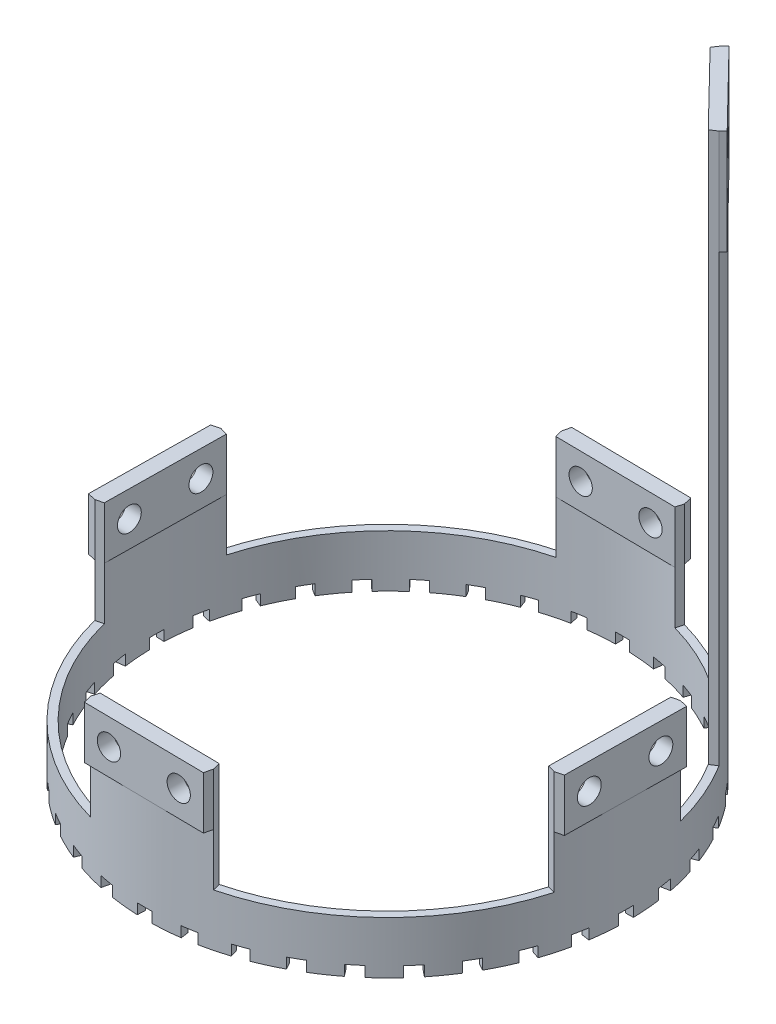
SolidWorks part; units mm, degrees
ref_plane "前视基准面" through (0, 0, 0) normal (0, 0, 1) x (1, 0, 0)
ref_plane "上视基准面" through (0, 0, 0) normal (0, 1, 0) x (1, 0, 0)
ref_plane "右视基准面" through (0, 0, 0) normal (1, 0, 0) x (0, 0, -1)
sketch "草图1" plane through (0, 0, 0) normal (0, 1, 0) x (1, 0, 0)
  circle A0 centre (0, 0) radius 46
  circle A1 centre (0, 0) radius 44.5
  dimension "D1" = 92
  dimension "D2" = 89
extrude "凸台-拉伸1" add sketch "草图1" along normal blind 10
sketch "草图2" plane through (0, 10, 0) normal (0, 1, 0) x (1, 0, 0)
  line L0 (-10.9731, 43.1259) -> (-11.343, 44.5796)
  line L1 (12.06, 42.8347) -> (12.4665, 44.2785)
  line L2 (43.1259, 10.9731) -> (44.5796, 11.343)
  line L3 (42.8347, -12.06) -> (44.2785, -12.4665)
  line L4 (10.9731, -43.1259) -> (11.343, -44.5796)
  line L5 (-12.06, -42.8347) -> (-12.4665, -44.2785)
  line L6 (-43.1259, -10.9731) -> (-44.5796, -11.343)
  line L7 (-42.8347, 12.06) -> (-44.2785, 12.4665)
  arc A0 (12.06, 42.8347) -> (-10.9731, 43.1259) centre (0, 0) ccw
  arc A1 (12.4665, 44.2785) -> (-11.343, 44.5796) centre (0, 0) ccw
  arc A2 (42.8347, -12.06) -> (43.1259, 10.9731) centre (0, 0) ccw
  arc A3 (44.2785, -12.4665) -> (44.5796, 11.343) centre (0, 0) ccw
  arc A4 (-12.06, -42.8347) -> (10.9731, -43.1259) centre (0, 0) ccw
  arc A5 (-12.4665, -44.2785) -> (11.343, -44.5796) centre (0, 0) ccw
  arc A6 (-42.8347, 12.06) -> (-43.1259, -10.9731) centre (0, 0) ccw
  arc A7 (-44.2785, 12.4665) -> (-44.5796, -11.343) centre (0, 0) ccw
  point P21 (0, 0)
  dimension "D1" = 30
  dimension "D2" = 4
extrude "凸台-拉伸2" add sketch "草图2" along normal blind 20
sketch "草图3" plane through (0, 30, 0) normal (0, 1, 0) x (1, 0, 0)
  line L16 (-10.9731, 46.1424) -> (-11.343, 44.5796)
  line L17 (-11.343, 44.5796) -> (-10.9731, 43.1259)
  line L18 (12.06, 45.8512) -> (12.4665, 44.2785)
  line L19 (12.06, 42.8347) -> (12.4665, 44.2785) construction
  line L20 (12.4665, 44.2785) -> (12.06, 42.8347)
  line L22 (44.2785, -12.4665) -> (42.8347, -12.06)
  line L23 (45.8512, -12.06) -> (44.2785, -12.4665)
  line L25 (46.1424, 10.9731) -> (44.5796, 11.343)
  line L26 (44.5796, 11.343) -> (43.1259, 10.9731)
  line L28 (-12.4665, -44.2785) -> (-12.06, -42.8347)
  line L29 (-12.06, -45.8512) -> (-12.4665, -44.2785)
  line L31 (10.9731, -46.1424) -> (11.343, -44.5796)
  line L32 (11.343, -44.5796) -> (10.9731, -43.1259)
  line L34 (-44.2785, 12.4665) -> (-42.8347, 12.06)
  line L35 (-45.8512, 12.06) -> (-44.2785, 12.4665)
  line L37 (-46.1424, -10.9731) -> (-44.5796, -11.343)
  line L38 (-44.5796, -11.343) -> (-43.1259, -10.9731)
  line L39 (-10.9731, 46.1424) -> (12.06, 45.8512)
  line L40 (12.06, 42.8347) -> (-10.9731, 43.1259)
  line L41 (-42.8347, 12.06) -> (-43.1259, -10.9731)
  line L42 (-46.1424, -10.9731) -> (-45.8512, 12.06)
  line L43 (10.9731, -43.1259) -> (-12.06, -42.8347)
  line L44 (-12.06, -45.8512) -> (10.9731, -46.1424)
  line L45 (43.1259, 10.9731) -> (42.8347, -12.06)
  line L46 (45.8512, -12.06) -> (46.1424, 10.9731)
  arc A0 (44.5796, 11.343) -> (12.4665, 44.2785) centre (0, 0) ccw construction
  point P24 (0, 0)
  point P51 (0, 0)
  dimension "D2" = 4
extrude "凸台-拉伸4" add sketch "草图3" against normal blind 10
sketch "草图5" plane through (-45.9963, 0, -0.5816) normal (-0.9999, 0, -0.0126) x (-0.0126, 0, 0.9999)
  line L0 (0.0381, 30) -> (0.0381, 5.2053) construction
  line L1 (-11.4793, 30) -> (11.5556, 30) construction
  line L2 (-46, 0) -> (46, 0) construction
  circle A0 centre (-6.7119, 25) radius 2.25
  circle A1 centre (6.7881, 25) radius 2.25
  dimension "D1" = 4.5
  dimension "D2" = 6.75
  dimension "D3" = 25
extrude "切除-拉伸1" cut sketch "草图5" against normal through all
sketch "草图6" plane through (-0.5816, 0, 45.9963) normal (-0.0126, 0, 0.9999) x (0.9999, 0, 0.0126)
  line L0 (0.0381, 30) -> (0, 0) construction
  line L1 (-11.4793, 30) -> (11.5556, 30) construction
  line L2 (-46, 0) -> (46, 0) construction
  circle A0 centre (-6.7182, 25) radius 2.25
  circle A1 centre (6.7818, 24.9828) radius 2.25
  dimension "D1" = 6.75
  dimension "D2" = 25
extrude "切除-拉伸2" cut sketch "草图6" against normal through all
sketch "草图7" plane through (0, 0, 0) normal (0, -1, 0) x (1, 0, 0)
  line L0 (-1.7737, 44.4646) -> (-1.8335, 45.9634)
  line L1 (0.9441, 44.49) -> (0.9759, 45.9896)
  line L2 (5.9744, 44.0971) -> (6.1758, 45.5835)
  line L3 (8.6553, 43.6501) -> (8.9471, 45.1215)
  line L4 (13.541, 42.3897) -> (13.9975, 43.8186)
  line L5 (16.1036, 41.484) -> (16.6464, 42.8824)
  line L6 (20.6962, 39.3944) -> (21.3938, 40.7223)
  line L7 (23.0626, 38.0574) -> (23.84, 39.3403)
  line L8 (27.2225, 35.202) -> (28.1402, 36.3886)
  line L9 (29.3208, 33.4745) -> (30.3091, 34.6028)
  line L10 (32.9217, 29.9401) -> (34.0315, 30.9493)
  line L11 (34.6881, 27.8744) -> (35.8574, 28.814)
  line L12 (37.6206, 23.7684) -> (38.8887, 24.5696)
  line L13 (39.0015, 21.4274) -> (40.3161, 22.1497)
  line L14 (41.1764, 16.8746) -> (42.5644, 17.4434)
  line L15 (42.1298, 14.3293) -> (43.5499, 14.8124)
  line L16 (43.4811, 9.468) -> (44.9468, 9.7871)
  line L17 (43.978, 6.7959) -> (45.4604, 7.025)
  line L18 (44.4646, 1.7737) -> (45.9634, 1.8335)
  line L19 (44.49, -0.9441) -> (45.9896, -0.9759)
  line L20 (44.0971, -5.9744) -> (45.5835, -6.1758)
  line L21 (43.6501, -8.6553) -> (45.1215, -8.9471)
  line L22 (42.3897, -13.541) -> (43.8186, -13.9975)
  line L23 (41.484, -16.1036) -> (42.8824, -16.6464)
  line L24 (39.3944, -20.6962) -> (40.7223, -21.3938)
  line L25 (38.0574, -23.0626) -> (39.3403, -23.84)
  line L26 (35.202, -27.2225) -> (36.3886, -28.1402)
  line L27 (33.4745, -29.3208) -> (34.6028, -30.3091)
  line L28 (29.9401, -32.9217) -> (30.9493, -34.0315)
  line L29 (27.8744, -34.6881) -> (28.814, -35.8574)
  line L30 (23.7684, -37.6206) -> (24.5696, -38.8887)
  line L31 (21.4274, -39.0015) -> (22.1497, -40.3161)
  line L32 (16.8746, -41.1764) -> (17.4434, -42.5644)
  line L33 (14.3293, -42.1298) -> (14.8124, -43.5499)
  line L34 (9.468, -43.4811) -> (9.7871, -44.9468)
  line L35 (6.7959, -43.978) -> (7.025, -45.4604)
  line L36 (1.7737, -44.4646) -> (1.8335, -45.9634)
  line L37 (-0.9441, -44.49) -> (-0.9759, -45.9896)
  line L38 (-5.9744, -44.0971) -> (-6.1758, -45.5835)
  line L39 (-8.6553, -43.6501) -> (-8.9471, -45.1215)
  line L40 (-13.541, -42.3897) -> (-13.9975, -43.8186)
  line L41 (-16.1036, -41.484) -> (-16.6464, -42.8824)
  line L42 (-20.6962, -39.3944) -> (-21.3938, -40.7223)
  line L43 (-23.0626, -38.0574) -> (-23.84, -39.3403)
  line L44 (-27.2225, -35.202) -> (-28.1402, -36.3886)
  line L45 (-29.3208, -33.4745) -> (-30.3091, -34.6028)
  line L46 (-32.9217, -29.9401) -> (-34.0315, -30.9493)
  line L47 (-34.6881, -27.8744) -> (-35.8574, -28.814)
  line L48 (-37.6206, -23.7684) -> (-38.8887, -24.5696)
  line L49 (-39.0015, -21.4274) -> (-40.3161, -22.1497)
  line L50 (-41.1764, -16.8746) -> (-42.5644, -17.4434)
  line L51 (-42.1298, -14.3293) -> (-43.5499, -14.8124)
  line L52 (-43.4811, -9.468) -> (-44.9468, -9.7871)
  line L53 (-43.978, -6.7959) -> (-45.4604, -7.025)
  line L54 (-44.4646, -1.7737) -> (-45.9634, -1.8335)
  line L55 (-44.49, 0.9441) -> (-45.9896, 0.9759)
  line L56 (-44.0971, 5.9744) -> (-45.5835, 6.1758)
  line L57 (-43.6501, 8.6553) -> (-45.1215, 8.9471)
  line L58 (-42.3897, 13.541) -> (-43.8186, 13.9975)
  line L59 (-41.484, 16.1036) -> (-42.8824, 16.6464)
  line L60 (-39.3944, 20.6962) -> (-40.7223, 21.3938)
  line L61 (-38.0574, 23.0626) -> (-39.3403, 23.84)
  line L62 (-35.202, 27.2225) -> (-36.3886, 28.1402)
  line L63 (-33.4745, 29.3208) -> (-34.6028, 30.3091)
  line L64 (-29.9401, 32.9217) -> (-30.9493, 34.0315)
  line L65 (-27.8744, 34.6881) -> (-28.814, 35.8574)
  line L66 (-23.7684, 37.6206) -> (-24.5696, 38.8887)
  line L67 (-21.4274, 39.0015) -> (-22.1497, 40.3161)
  line L68 (-16.8746, 41.1764) -> (-17.4434, 42.5644)
  line L69 (-14.3293, 42.1298) -> (-14.8124, 43.5499)
  line L70 (-9.468, 43.4811) -> (-9.7871, 44.9468)
  line L71 (-6.7959, 43.978) -> (-7.025, 45.4604)
  circle A0 centre (0, 0) radius 46 construction
  arc A1 (0.9441, 44.49) -> (-1.7737, 44.4646) centre (0, 0) ccw
  arc A2 (0.9759, 45.9896) -> (-1.8335, 45.9634) centre (0, 0) ccw
  arc A3 (8.9471, 45.1215) -> (6.1758, 45.5835) centre (0, 0) ccw
  arc A4 (8.6553, 43.6501) -> (5.9744, 44.0971) centre (0, 0) ccw
  arc A5 (16.6464, 42.8824) -> (13.9975, 43.8186) centre (0, 0) ccw
  arc A6 (16.1036, 41.484) -> (13.541, 42.3897) centre (0, 0) ccw
  arc A7 (23.84, 39.3403) -> (21.3938, 40.7223) centre (0, 0) ccw
  arc A8 (23.0626, 38.0574) -> (20.6962, 39.3944) centre (0, 0) ccw
  arc A9 (30.3091, 34.6028) -> (28.1402, 36.3886) centre (0, 0) ccw
  arc A10 (29.3208, 33.4745) -> (27.2225, 35.202) centre (0, 0) ccw
  arc A11 (35.8574, 28.814) -> (34.0315, 30.9493) centre (0, 0) ccw
  arc A12 (34.6881, 27.8744) -> (32.9217, 29.9401) centre (0, 0) ccw
  arc A13 (40.3161, 22.1497) -> (38.8887, 24.5696) centre (0, 0) ccw
  arc A14 (39.0015, 21.4274) -> (37.6206, 23.7684) centre (0, 0) ccw
  arc A15 (43.5499, 14.8124) -> (42.5644, 17.4434) centre (0, 0) ccw
  arc A16 (42.1298, 14.3293) -> (41.1764, 16.8746) centre (0, 0) ccw
  arc A17 (45.4604, 7.025) -> (44.9468, 9.7871) centre (0, 0) ccw
  arc A18 (43.978, 6.7959) -> (43.4811, 9.468) centre (0, 0) ccw
  arc A19 (45.9896, -0.9759) -> (45.9634, 1.8335) centre (0, 0) ccw
  arc A20 (44.49, -0.9441) -> (44.4646, 1.7737) centre (0, 0) ccw
  arc A21 (45.1215, -8.9471) -> (45.5835, -6.1758) centre (0, 0) ccw
  arc A22 (43.6501, -8.6553) -> (44.0971, -5.9744) centre (0, 0) ccw
  arc A23 (42.8824, -16.6464) -> (43.8186, -13.9975) centre (0, 0) ccw
  arc A24 (41.484, -16.1036) -> (42.3897, -13.541) centre (0, 0) ccw
  arc A25 (39.3403, -23.84) -> (40.7223, -21.3938) centre (0, 0) ccw
  arc A26 (38.0574, -23.0626) -> (39.3944, -20.6962) centre (0, 0) ccw
  arc A27 (34.6028, -30.3091) -> (36.3886, -28.1402) centre (0, 0) ccw
  arc A28 (33.4745, -29.3208) -> (35.202, -27.2225) centre (0, 0) ccw
  arc A29 (28.814, -35.8574) -> (30.9493, -34.0315) centre (0, 0) ccw
  arc A30 (27.8744, -34.6881) -> (29.9401, -32.9217) centre (0, 0) ccw
  arc A31 (22.1497, -40.3161) -> (24.5696, -38.8887) centre (0, 0) ccw
  arc A32 (21.4274, -39.0015) -> (23.7684, -37.6206) centre (0, 0) ccw
  arc A33 (14.8124, -43.5499) -> (17.4434, -42.5644) centre (0, 0) ccw
  arc A34 (14.3293, -42.1298) -> (16.8746, -41.1764) centre (0, 0) ccw
  arc A35 (7.025, -45.4604) -> (9.7871, -44.9468) centre (0, 0) ccw
  arc A36 (6.7959, -43.978) -> (9.468, -43.4811) centre (0, 0) ccw
  arc A37 (-0.9759, -45.9896) -> (1.8335, -45.9634) centre (0, 0) ccw
  arc A38 (-0.9441, -44.49) -> (1.7737, -44.4646) centre (0, 0) ccw
  arc A39 (-8.9471, -45.1215) -> (-6.1758, -45.5835) centre (0, 0) ccw
  arc A40 (-8.6553, -43.6501) -> (-5.9744, -44.0971) centre (0, 0) ccw
  arc A41 (-16.6464, -42.8824) -> (-13.9975, -43.8186) centre (0, 0) ccw
  arc A42 (-16.1036, -41.484) -> (-13.541, -42.3897) centre (0, 0) ccw
  arc A43 (-23.84, -39.3403) -> (-21.3938, -40.7223) centre (0, 0) ccw
  arc A44 (-23.0626, -38.0574) -> (-20.6962, -39.3944) centre (0, 0) ccw
  arc A45 (-30.3091, -34.6028) -> (-28.1402, -36.3886) centre (0, 0) ccw
  arc A46 (-29.3208, -33.4745) -> (-27.2225, -35.202) centre (0, 0) ccw
  arc A47 (-35.8574, -28.814) -> (-34.0315, -30.9493) centre (0, 0) ccw
  arc A48 (-34.6881, -27.8744) -> (-32.9217, -29.9401) centre (0, 0) ccw
  arc A49 (-40.3161, -22.1497) -> (-38.8887, -24.5696) centre (0, 0) ccw
  arc A50 (-39.0015, -21.4274) -> (-37.6206, -23.7684) centre (0, 0) ccw
  arc A51 (-43.5499, -14.8124) -> (-42.5644, -17.4434) centre (0, 0) ccw
  arc A52 (-42.1298, -14.3293) -> (-41.1764, -16.8746) centre (0, 0) ccw
  arc A53 (-45.4604, -7.025) -> (-44.9468, -9.7871) centre (0, 0) ccw
  arc A54 (-43.978, -6.7959) -> (-43.4811, -9.468) centre (0, 0) ccw
  arc A55 (-45.9896, 0.9759) -> (-45.9634, -1.8335) centre (0, 0) ccw
  arc A56 (-44.49, 0.9441) -> (-44.4646, -1.7737) centre (0, 0) ccw
  arc A57 (-45.1215, 8.9471) -> (-45.5835, 6.1758) centre (0, 0) ccw
  arc A58 (-43.6501, 8.6553) -> (-44.0971, 5.9744) centre (0, 0) ccw
  arc A59 (-42.8824, 16.6464) -> (-43.8186, 13.9975) centre (0, 0) ccw
  arc A60 (-41.484, 16.1036) -> (-42.3897, 13.541) centre (0, 0) ccw
  arc A61 (-39.3403, 23.84) -> (-40.7223, 21.3938) centre (0, 0) ccw
  arc A62 (-38.0574, 23.0626) -> (-39.3944, 20.6962) centre (0, 0) ccw
  arc A63 (-34.6028, 30.3091) -> (-36.3886, 28.1402) centre (0, 0) ccw
  arc A64 (-33.4745, 29.3208) -> (-35.202, 27.2225) centre (0, 0) ccw
  arc A65 (-28.814, 35.8574) -> (-30.9493, 34.0315) centre (0, 0) ccw
  arc A66 (-27.8744, 34.6881) -> (-29.9401, 32.9217) centre (0, 0) ccw
  arc A67 (-22.1497, 40.3161) -> (-24.5696, 38.8887) centre (0, 0) ccw
  arc A68 (-21.4274, 39.0015) -> (-23.7684, 37.6206) centre (0, 0) ccw
  arc A69 (-14.8124, 43.5499) -> (-17.4434, 42.5644) centre (0, 0) ccw
  arc A70 (-14.3293, 42.1298) -> (-16.8746, 41.1764) centre (0, 0) ccw
  arc A71 (-7.025, 45.4604) -> (-9.7871, 44.9468) centre (0, 0) ccw
  arc A72 (-6.7959, 43.978) -> (-9.468, 43.4811) centre (0, 0) ccw
  point P151 (0, 0)
  dimension "D1" = 3.5
  dimension "D2" = 36
extrude "切除-拉伸3" cut sketch "草图7" against normal blind 2
sketch "草图8" plane through (0, 10, 0) normal (0, 1, 0) x (1, 0, 0)
  line L0 (0, 0) -> (32.9355, 32.1131) construction
  line L1 (0, 0) -> (25.2043, 38.4804) construction
  line L2 (0, 0) -> (39.1054, 24.2233) construction
  line L3 (25.2043, 38.4804) -> (39.1054, 24.2233) construction
  line L4 (25.2043, 38.4804) -> (24.3824, 37.2256)
  line L5 (39.1054, 24.2233) -> (37.8302, 23.4334)
  arc A0 (44.5796, 11.343) -> (12.4665, 44.2785) centre (0, 0) ccw construction
  arc A1 (43.1259, 10.9731) -> (12.06, 42.8347) centre (0, 0) ccw construction
  arc A2 (37.8302, 23.4334) -> (24.3824, 37.2256) centre (0, 0) ccw
  arc A3 (39.1054, 24.2233) -> (25.2043, 38.4804) centre (0, 0) ccw
  dimension "D1" = 25
extrude "凸台-拉伸6" add sketch "草图8" along normal blind 105
sketch "草图9" plane through (0, 115, 0) normal (0, 1, 0) x (1, 0, 0)
  line L0 (24.3824, 37.2256) -> (37.8302, 23.4334)
  line L1 (25.985, 39.2416) -> (39.8861, 24.9845)
  line L2 (25.2043, 38.4804) -> (25.985, 39.2416)
  line L3 (39.1054, 24.2233) -> (39.8861, 24.9845)
  line L4 (24.3824, 37.2256) -> (25.2043, 38.4804)
  line L5 (37.8302, 23.4334) -> (39.1054, 24.2233)
  arc A0 (39.1054, 24.2233) -> (25.2043, 38.4804) centre (0, 0) ccw construction
extrude "凸台-拉伸7" add sketch "草图9" against normal blind 20
sketch "草图10" plane through (32.9355, 0, -32.1131) normal (0.716, 0, -0.6981) x (-0.6981, 0, -0.716)
  line L0 (0, 115) -> (0, 95) construction
  line L1 (-9.9562, 115) -> (9.9562, 115) construction
  line L2 (0, 105) -> (-4.9497, 109.9497) construction
  circle A0 centre (0, 105) radius 3
  circle A1 centre (-4.9497, 109.9497) radius 1.6
  circle A2 centre (-4.9497, 100.0503) radius 1.6
  circle A3 centre (4.9497, 100.0503) radius 1.6
  circle A4 centre (4.9497, 109.9497) radius 1.6
  point P18 (0, 105)
  dimension "D1" = 10
  dimension "D4" = 4
  dimension "D2" = 7
  dimension "D3" = 45
extrude "切除-拉伸4" cut sketch "草图10" against normal blind 20
equation "\"20、\"=42"
